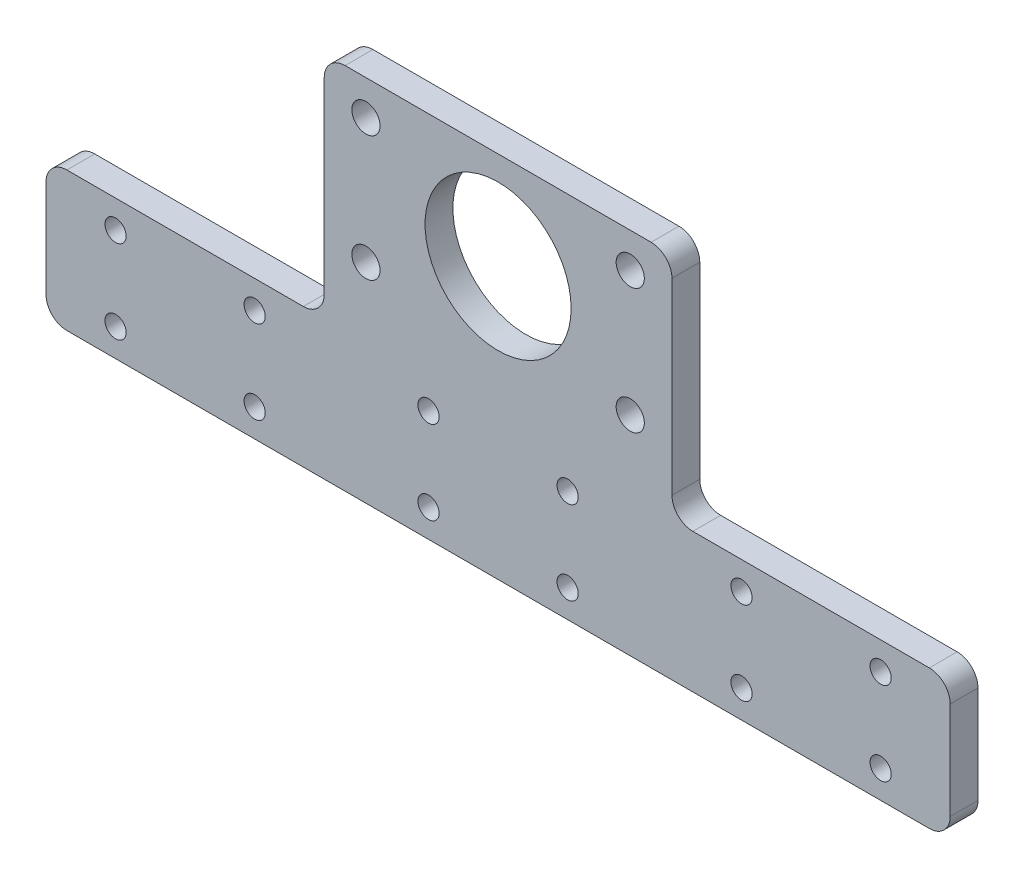
SolidWorks part; units mm, degrees
material "Thornel Mat VMA"
ref_plane "前视基准面" through (0, 0, 0) normal (0, 0, 1) x (1, 0, 0)
ref_plane "上视基准面" through (0, 0, 0) normal (0, 1, 0) x (1, 0, 0)
ref_plane "右视基准面" through (0, 0, 0) normal (1, 0, 0) x (0, 0, -1)
other "Configuration Table"
sketch "草图1" plane through (0, 0, 0) normal (0, 0, 1) x (1, 0, 0)
  line L0 (-25, 0) -> (25, 0)
  line L1 (25, 0) -> (25, -33)
  line L2 (25, -33) -> (65, -33)
  line L3 (65, -33) -> (65, -53)
  line L4 (65, -53) -> (-65, -53)
  line L5 (-65, -53) -> (-65, -33)
  line L6 (-65, -33) -> (-25, -33)
  line L7 (-25, -33) -> (-25, 0)
  line L8 (0, -53) -> (0, 0) construction
  dimension "D1" = 20
  dimension "D2" = 50
  dimension "D3" = 33
  dimension "D4" = 130
extrude "凸台-拉伸1" add sketch "草图1" along normal mid plane 4
fillet "圆角1" radius 3 8 edges at (25, 0, 0) (25, -33, 0) (65, -33, 0) (65, -53, 0) (-65, -53, 0) (-65, -33, 0) (-25, -33, 0) (-25, 0, 0)
sketch "草图2" plane through (0, 0, 2) normal (0, 0, 1) x (1, 0, 0)
  line L0 (-28, -33) -> (-62, -33) construction
  line L1 (-19, -23) -> (19, -23) construction
  line L2 (-19, -23) -> (-19, -5) construction
  line L3 (-19, -5) -> (19, -5) construction
  line L4 (19, -23) -> (19, -5) construction
  line L5 (-19, -23) -> (19, -5) construction
  line L6 (-19, -5) -> (19, -23) construction
  circle A0 centre (-19, -5) radius 2.025
  circle A1 centre (-19, -23) radius 2.025
  circle A2 centre (19, -5) radius 2.025
  circle A3 centre (19, -23) radius 2.025
  point P0 (0, -14)
  dimension "D1" = 4.05
  dimension "D2" = 38
  dimension "D3" = 18
  dimension "D4" = 10
extrude "切除-拉伸1" cut sketch "草图2" against normal through all both and the other way through all
sketch "草图3" plane through (0, 0, -2) normal (0, 0, -1) x (-1, 0, 0)
  line L0 (62, -53) -> (-62, -53) construction
  line L1 (0, 0) -> (0, -52) construction
  line L2 (-149.5, -52) -> (149.5, -52) construction
  line L3 (-45, -33) -> (-45, -53) construction
  line L4 (-62, -33) -> (-28, -33) construction
  line L5 (45, -33) -> (45, -53) construction
  line L6 (28, -33) -> (62, -33) construction
  line L7 (-65, -43) -> (65, -43) construction
  line L8 (-65, -50) -> (-65, -36) construction
  line L9 (65, -36) -> (65, -50) construction
  line L10 (0, -86) -> (0, -34) construction
  circle A0 centre (-55, -49) radius 1.525
  circle A1 centre (-35, -49) radius 1.525
  circle A2 centre (-10, -49) radius 1.525
  circle A3 centre (10, -49) radius 1.525
  circle A4 centre (35, -49) radius 1.525
  circle A5 centre (55, -49) radius 1.525
  circle A6 centre (55, -37) radius 1.525
  circle A7 centre (35, -37) radius 1.525
  circle A8 centre (10, -37) radius 1.525
  circle A9 centre (-10, -37) radius 1.525
  circle A10 centre (-35, -37) radius 1.525
  circle A11 centre (-55, -37) radius 1.525
  dimension "D1" = 3.05
  dimension "D2" = 20
  dimension "D3" = 20
  dimension "D4" = 20
  dimension "D5" = 4
extrude "切除-拉伸2" cut sketch "草图3" against normal blind 10
sketch "草图4" plane through (0, 0, 2) normal (0, 0, 1) x (1, 0, 0)
  line L1 (-19, -5) -> (-19, -23) construction
  line L2 (0, -14) -> (-19, -14) construction
  circle A0 centre (0, -14) radius 10.5
  dimension "D1" = 21
extrude "切除-拉伸3" cut sketch "草图4" against normal through all
